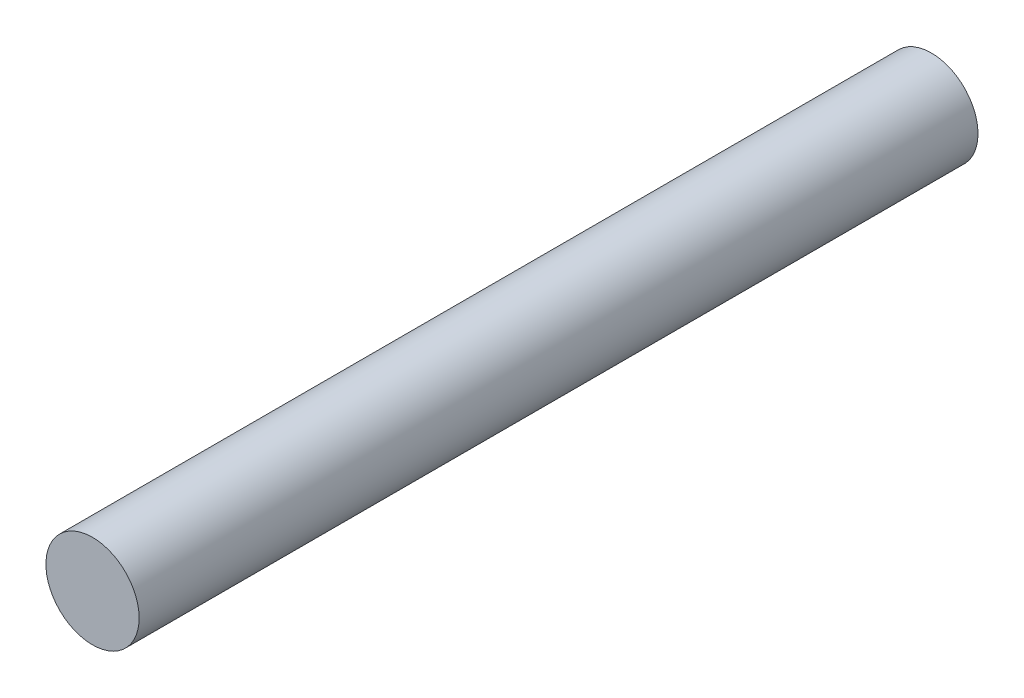
SolidWorks part; units mm, degrees
ref_plane "前视基准面" through (0, 0, 0) normal (0, 0, 1) x (1, 0, 0)
ref_plane "上视基准面" through (0, 0, 0) normal (0, 1, 0) x (1, 0, 0)
ref_plane "右视基准面" through (0, 0, 0) normal (1, 0, 0) x (0, 0, -1)
sketch "草图1" plane through (0, 0, 0) normal (0, 0, 1) x (1, 0, 0)
  circle A0 centre (0, 0) radius 1
extrude "凸台-拉伸1" add sketch "草图1" along normal blind 18
